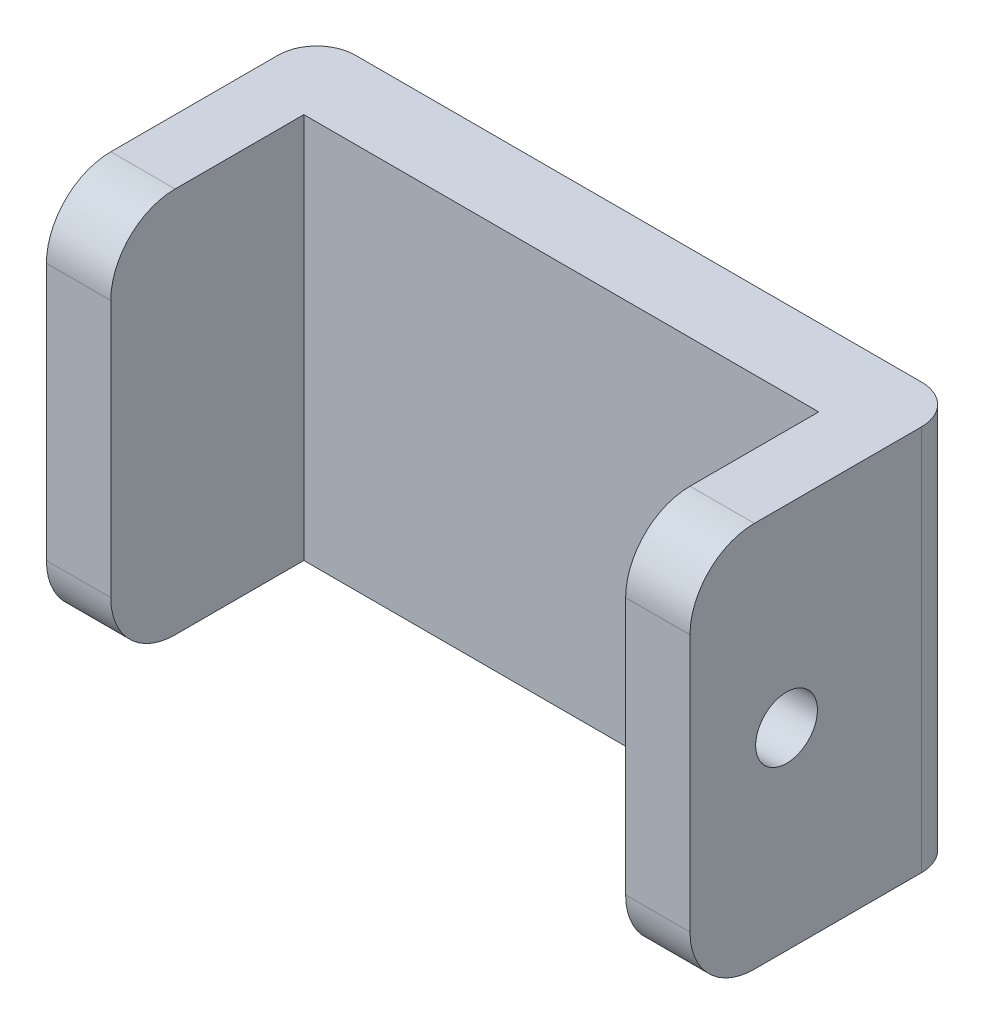
SolidWorks part; units mm, degrees
ref_plane "Front Plane" through (0, 0, 0) normal (0, 0, 1) x (1, 0, 0)
ref_plane "Top Plane" through (0, 0, 0) normal (0, 1, 0) x (1, 0, 0)
ref_plane "Right Plane" through (0, 0, 0) normal (1, 0, 0) x (0, 0, -1)
sketch "Sketch1" plane through (0, 0, 0) normal (0, 0, 1) x (1, 0, 0)
  line L0 (-281.5, -68.8259) -> (-281.5, -28.8259) construction
  line L1 (-286.5, -33) -> (-236.5, -33)
  line L2 (-286.5, -33) -> (-286.5, -63)
  line L3 (-286.5, -63) -> (-236.5, -63)
  line L4 (-236.5, -33) -> (-236.5, -63)
  dimension "D1" = 5
  dimension "D2" = 50
  dimension "D4" = 30
extrude "Boss-Extrude1" add sketch "Sketch1" along normal blind 6
sketch "Sketch3" plane through (0, 0, 6) normal (0, 0, 1) x (1, 0, 0)
  line L0 (-261.5, -33) -> (-261.5, -63) construction
  line L1 (-236.5, -63) -> (-241.5, -63)
  line L2 (-236.5, -63) -> (-236.5, -33)
  line L3 (-236.5, -33) -> (-241.5, -33)
  line L4 (-241.5, -63) -> (-241.5, -33)
  line L5 (-236.5, -33) -> (-286.5, -33) construction
  line L6 (-286.5, -63) -> (-236.5, -63) construction
  line L7 (-281.5, -63) -> (-281.5, -33)
  line L8 (-286.5, -33) -> (-281.5, -33)
  line L9 (-286.5, -63) -> (-286.5, -33)
  line L10 (-286.5, -63) -> (-281.5, -63)
extrude "Boss-Extrude2" add sketch "Sketch3" along normal blind 15
sketch "Sketch4" plane through (-236.5, 0, 0) normal (1, 0, 0) x (0, 0, -1)
  line L0 (-21, -48) -> (0, -48) construction
  line L1 (-21, -63) -> (-21, -33) construction
  line L2 (0, -63) -> (0, -33) construction
  circle A0 centre (-13.5, -48) radius 2.4
extrude "Cut-Extrude1" cut sketch "Sketch4" against normal up to surface (5 mm away) up to face at (-241.5, -48, 13.5)
fillet "Fillet2" radius 3 2 edges at (-236.5, -48, 0) (-286.5, -48, 0)
fillet "Fillet3" radius 5 4 edges at (-239, -63, 21) (-239, -33, 21) (-284, -63, 21) (-284, -33, 21)
